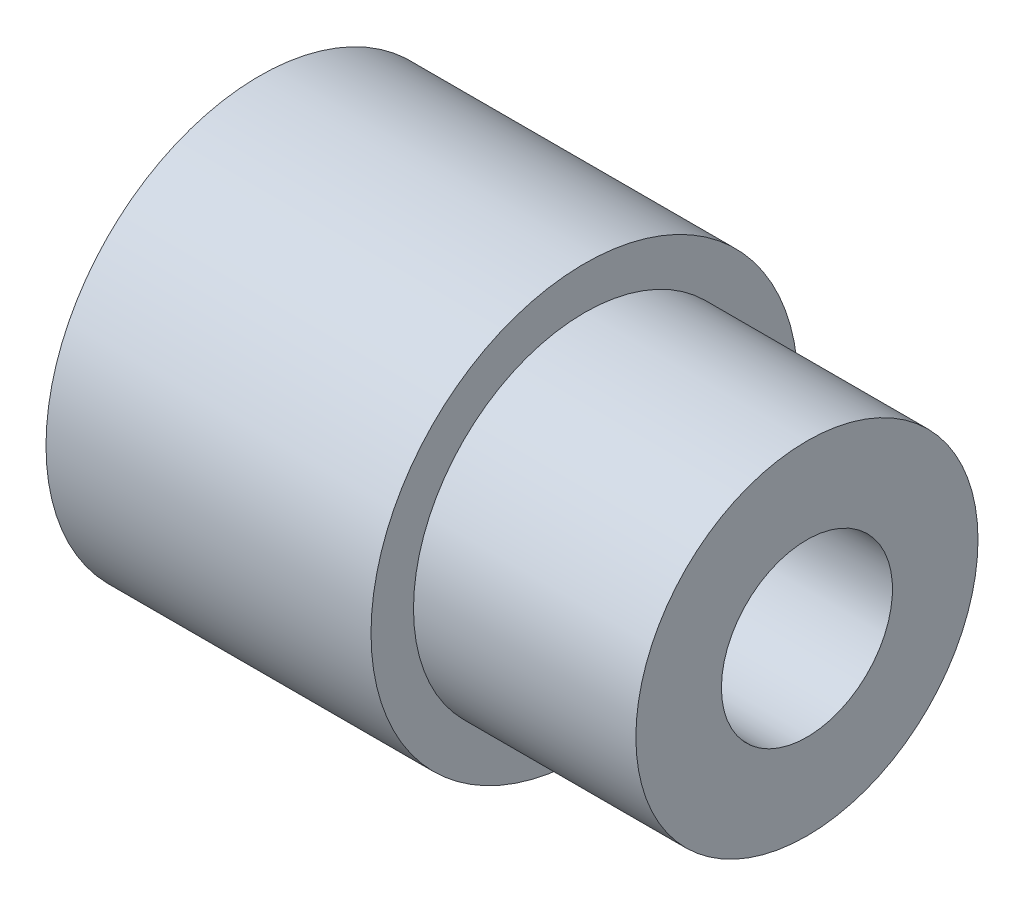
SolidWorks part; units mm, degrees
ref_plane "Front Plane" through (0, 0, 0) normal (0, 0, 1) x (1, 0, 0)
ref_plane "Top Plane" through (0, 0, 0) normal (0, 1, 0) x (1, 0, 0)
ref_plane "Right Plane" through (0, 0, 0) normal (1, 0, 0) x (0, 0, -1)
sketch "Sketch1" plane through (0, 0, 0) normal (0, 0, 1) x (1, 0, 0)
  line L0 (-17.2291, 0) -> (32.0849, 0) construction
  line L1 (-32, 9.4837) -> (-32, 12.4837)
  line L2 (-32, 12.4837) -> (-13, 12.4837)
  line L3 (-13, 12.4837) -> (-13, 10)
  line L4 (-13, 10) -> (0, 10)
  line L5 (0, 10) -> (0, 5)
  line L6 (-32, 9.4837) -> (-26, 9.4837)
  line L7 (-26, 9.4837) -> (-26, 7.4837)
  line L8 (-26, 7.4837) -> (-16, 7.4837)
  line L9 (-16, 7.4837) -> (-16, 5)
  line L10 (-16, 5) -> (0, 5)
  dimension "D1" = 5
  dimension "D2" = 5
  dimension "D3" = 3
  dimension "D4" = 32
  dimension "D5" = 13
  dimension "D6" = 2
  dimension "D7" = 6
  dimension "D8" = 10
revolve "Revolve1" add sketch "Sketch1" angle 360 about L0
